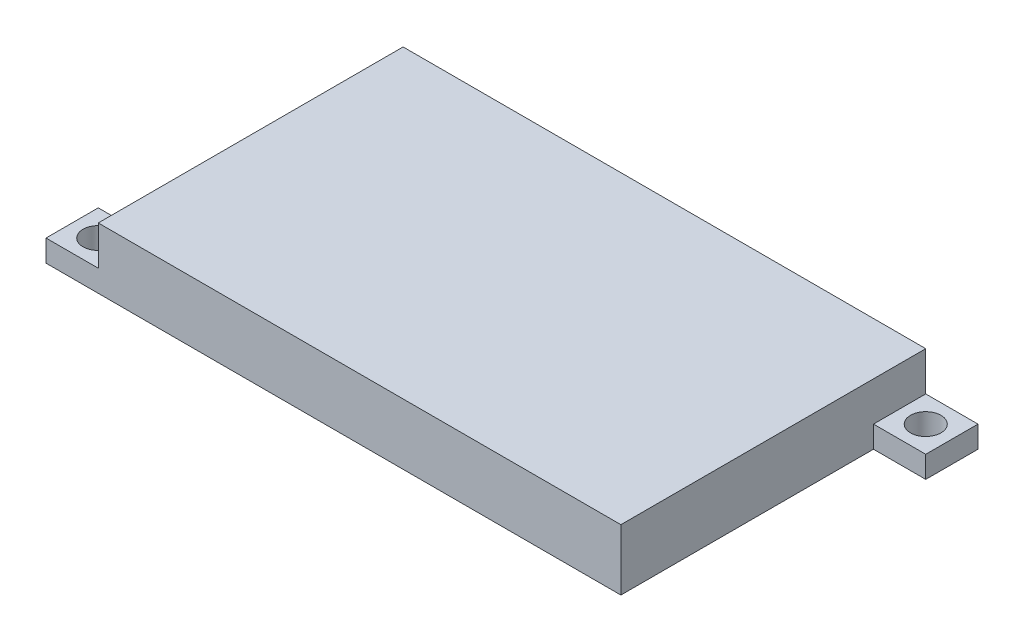
SolidWorks part; units mm, degrees
ref_plane "Front Plane" through (0, 0, 0) normal (0, 0, 1) x (1, 0, 0)
ref_plane "Top Plane" through (0, 0, 0) normal (0, 1, 0) x (1, 0, 0)
ref_plane "Right Plane" through (0, 0, 0) normal (1, 0, 0) x (0, 0, -1)
sketch "Sketch1" plane through (0, 0, 0) normal (0, 1, 0) x (1, 0, 0)
  line L0 (30, 17.5) -> (-30, 17.5)
  line L1 (30, 17.5) -> (30, -17.5)
  line L2 (30, -17.5) -> (-30, -17.5)
  line L3 (-30, 17.5) -> (-30, -17.5)
extrude "Boss-Extrude1" add sketch "Sketch1" along normal blind 7
sketch "Sketch3" plane through (0, 0, 0) normal (0, 1, 0) x (1, 0, 0)
  line L12 (-36, -11.5) -> (-30, -11.5)
  line L13 (-36, -17.5) -> (-36, -11.5)
  line L14 (-30, -17.5) -> (-36, -17.5)
  line L15 (-30, -11.5) -> (-30, -17.5)
  line L16 (30, 11.5) -> (30, 17.5)
  line L17 (30, 17.5) -> (36, 17.5)
  line L18 (36, 17.5) -> (36, 11.5)
  line L19 (36, 11.5) -> (30, 11.5)
  circle A2 centre (-33, -14.5) radius 1.75
  circle A3 centre (33, 14.5) radius 1.75
  dimension "D1" = 3.5
  dimension "D2" = 3.5
extrude "Boss-Extrude2" add sketch "Sketch3" along normal blind 2.5
sketch "Sketch4" plane through (0, 0, 0) normal (0, -1, 0) x (-1, 0, 0)
  line L1 (27.5, 15.5) -> (-27.5, 15.5)
  line L2 (27.5, 15.5) -> (27.5, -15.5)
  line L3 (27.5, -15.5) -> (-27.5, -15.5)
  line L4 (-27.5, 15.5) -> (-27.5, -15.5)
  line L5 (27.5, 15.5) -> (-27.5, -15.5) construction
  line L6 (27.5, -15.5) -> (-27.5, 15.5) construction
  point P0 (0, 0)
  dimension "D1" = 55
  dimension "D2" = 31
extrude "Cut-Extrude1" cut sketch "Sketch4" against normal blind 5
